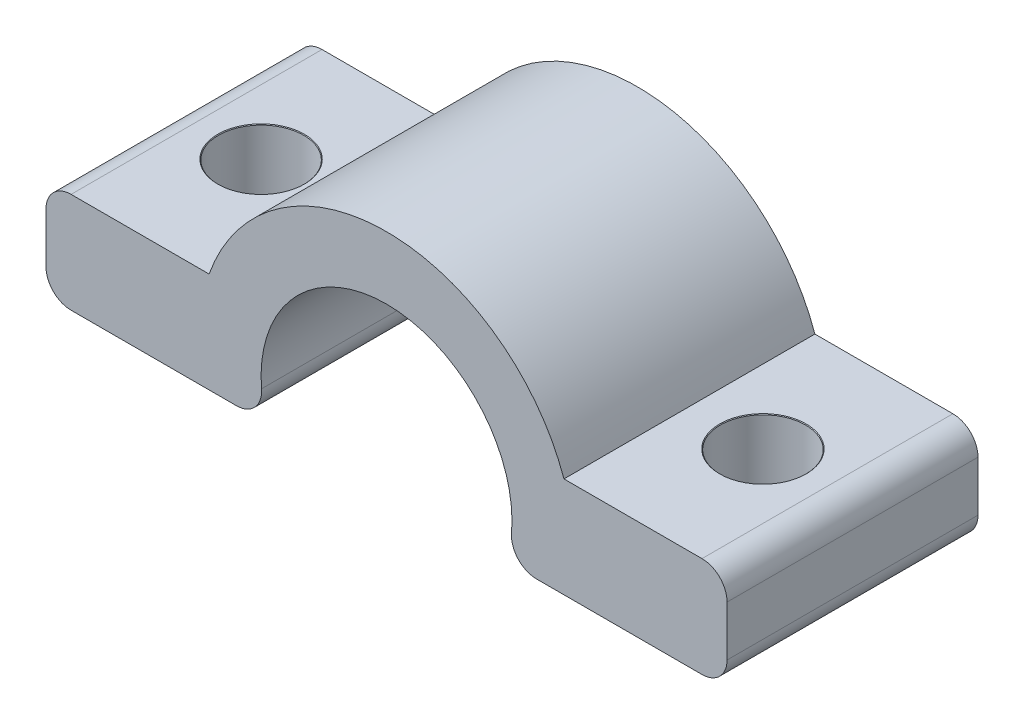
SolidWorks part; units mm, degrees
ref_plane "Front Plane" through (0, 0, 0) normal (0, 0, 1) x (1, 0, 0)
ref_plane "Top Plane" through (0, 0, 0) normal (0, 1, 0) x (1, 0, 0)
ref_plane "Right Plane" through (0, 0, 0) normal (1, 0, 0) x (0, 0, -1)
sketch "Sketch2" plane through (0, 0, 0) normal (0, 0, 1) x (1, 0, 0)
  line L0 (4.7697, -1.5) -> (13.5711, -1.5)
  line L1 (13.5711, -1.5) -> (13.5711, 2.5)
  line L2 (13.5711, 2.5) -> (7.0711, 2.5)
  line L3 (0, 7.5) -> (0, -7.5) construction
  line L5 (-7.0711, 2.5) -> (-13.5711, 2.5)
  line L6 (-13.5711, 2.5) -> (-13.5711, -1.5)
  line L7 (-13.5711, -1.5) -> (-4.7697, -1.5)
  arc A0 (4.7697, -1.5) -> (-4.7697, -1.5) centre (0, 0) ccw
  arc A2 (7.0711, 2.5) -> (-7.0711, 2.5) centre (0, 0) ccw
  point P10 (4.9749, -0.5)
  point P12 (-4.9749, 0.5)
  point P14 (4.9749, 0.5)
  dimension "D1" = 10
  dimension "D2" = 6.5
  dimension "D3" = 7.5
  dimension "D4" = 4
  dimension "D5" = 5
extrude "Boss-Extrude1" add sketch "Sketch2" along normal blind 10
sketch "Sketch4" plane through (0, 2.5, 0) normal (0, 1, 0) x (1, 0, 0)
  line L0 (-13.5711, -5) -> (13.5711, -5) construction
  line L1 (-13.5711, -10) -> (-13.5711, 0) construction
  line L2 (13.5711, -10) -> (13.5711, 0) construction
  line L3 (-10, -5) -> (10, -5)
  point P6 (-10, -5)
  point P7 (10, -5)
  point P8 (9.5, -5)
  point P11 (0, -5)
  point P12 (-9.5, -5)
  dimension "D1" = 20
hole_wizard "M3 Clearance Hole1" positions "Sketch5" profile "Sketch6" hole size "M3" standard "ANSI Metric" end condition through all
sketch "Sketch5" plane through (0, 2.5, 0) normal (0, 1, 0) x (1, 0, 0)
  point P0 (-10, -5)
  point P3 (10, -5)
sketch "Sketch6" plane through (-10, 2.5, 5) normal (1, 0, 0) x (0, 0, 1)
  line L0 (0, 0) -> (0, 4)
  line L1 (0, 4) -> (1.7, 4)
  line L2 (1.7, 4) -> (1.7, 0.025)
  line L3 (1.7, 0.025) -> (1.725, 0)
  line L5 (1.725, 0) -> (0, 0)
  line L6 (-1.7, 0.025) -> (-1.725, 0) construction
  line L11 (0, -6.35) -> (0, 107.95) construction
  dimension "Thru Hole Dia." = 3.4
  dimension "Thru Hole Depth" = 4
  dimension "Near C'Sink Dia." = 3.45
  dimension "Near C'Sink Angle" = 90
fillet "Fillet1" radius 1 6 edges at (13.5711, 2.5, 5) (13.5711, -1.5, 5) (-13.5711, -1.5, 5) (-13.5711, 2.5, 5) (4.7697, -1.5, 5) (-4.7697, -1.5, 5)
